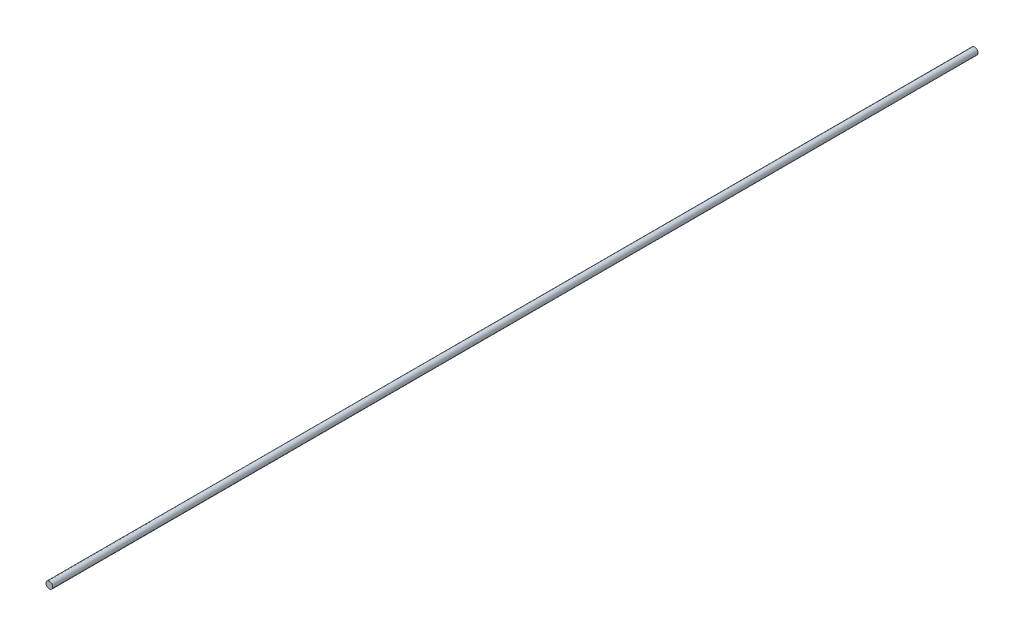
SolidWorks part; units mm, degrees
material "AISI 304"
ref_plane "Front Plane" through (0, 0, 0) normal (0, 0, 1) x (1, 0, 0)
ref_plane "Top Plane" through (0, 0, 0) normal (0, 1, 0) x (1, 0, 0)
ref_plane "Right Plane" through (0, 0, 0) normal (1, 0, 0) x (0, 0, -1)
sketch "Sketch1" plane through (0, 0, 0) normal (0, 0, 1) x (1, 0, 0)
  circle A0 centre (0, 0) radius 2.413
  dimension "D1" = 4.826
extrude "Boss-Extrude1" add sketch "Sketch1" along normal blind 660.4
